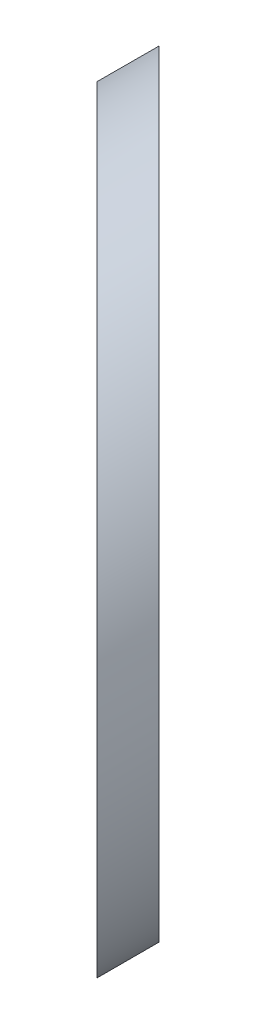
SolidWorks part; units mm, degrees
ref_plane "前视基准面" through (0, 0, 0) normal (0, 0, 1) x (1, 0, 0)
ref_plane "上视基准面" through (0, 0, 0) normal (0, 1, 0) x (1, 0, 0)
ref_plane "右视基准面" through (0, 0, 0) normal (1, 0, 0) x (0, 0, -1)
sketch "草图1" plane through (0, 0, 0) normal (0, 0, 1) x (1, 0, 0)
  circle A0 centre (0, 0) radius 6.25
  dimension "D1" = 12.5
extrude "凸台-拉伸1" add sketch "草图1" along normal blind 61
sketch "草图2" plane through (0, 0, 0) normal (0, 1, 0) x (1, 0, 0)
  line L0 (-39.3783, 21.3445) -> (32.9463, -50.9802)
  line L1 (-40.0854, 20.6374) -> (32.2392, -51.6873)
  line L2 (-40.0854, 20.6374) -> (-29.5005, -63.952)
  line L3 (-29.5005, -63.952) -> (29.8587, -63.952)
  line L4 (32.2392, -51.6873) -> (29.8587, -63.952)
  line L5 (32.9463, -50.9802) -> (32.9463, 3.7053)
  line L6 (32.9463, 3.7053) -> (-39.3783, 21.3445)
  line L7 (0, 0) -> (0, -25.8513) construction
  dimension "D2" = 135
  dimension "D1" = 1
extrude "切除-拉伸1" cut sketch "草图2" against normal mid plane 61
sketch "草图3" plane through (-9.0169, 0, 9.0169) normal (0.7071, 0, -0.7071) x (-0.7071, 0, -0.7071)
  line L0 (-21.5907, 0) -> (-3.913, 0) construction
  line L1 (-12.7519, 6.25) -> (-12.7519, -6.25) construction
  ellipse E0 centre (-12.7519, 0) end of major axis (-21.5907, 0) minor radius 6.25 construction
